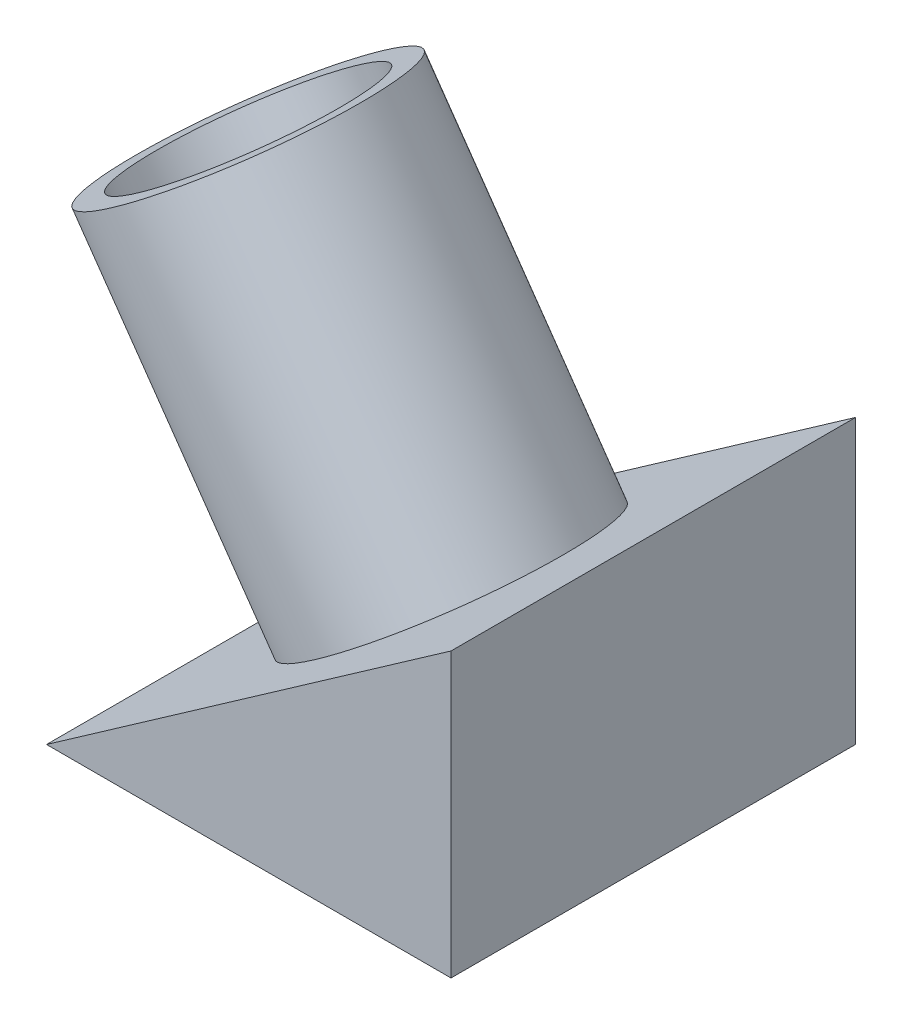
SolidWorks part; units mm, degrees
ref_plane "Front Plane" through (0, 0, 0) normal (0, 0, 1) x (1, 0, 0)
ref_plane "Top Plane" through (0, 0, 0) normal (0, 1, 0) x (1, 0, 0)
ref_plane "Right Plane" through (0, 0, 0) normal (1, 0, 0) x (0, 0, -1)
sketch "Sketch2" plane through (0, 0, 0) normal (0, 0, 1) x (1, 0, 0)
  line L0 (0, 0) -> (40, 28.0083)
  line L1 (40, 28.0083) -> (40, 0)
  line L2 (40, 0) -> (0, 0)
  dimension "D1" = 35
  dimension "D2" = 40
extrude "Boss-Extrude1" add sketch "Sketch2" along normal blind 40
sketch "Sketch3" plane through (0, 0, 0) normal (-0.5736, 0.8192, 0) x (0.8192, 0.5736, 0)
  line L0 (0, -40) -> (0, 0) construction
  circle A0 centre (24.415, -19.9837) radius 13.5
  dimension "D1" = 27
  dimension "D2" = 24.415
extrude "Boss-Extrude2" add sketch "Sketch3" along normal blind 35
sketch "Sketch4" plane through (-20.0752, 28.6703, 0) normal (-0.5736, 0.8192, 0) x (0.8192, 0.5736, 0)
  circle A0 centre (24.415, -19.9837) radius 11
  dimension "D1" = 22
extrude "Cut-Extrude1" cut sketch "Sketch4" against normal blind 35
